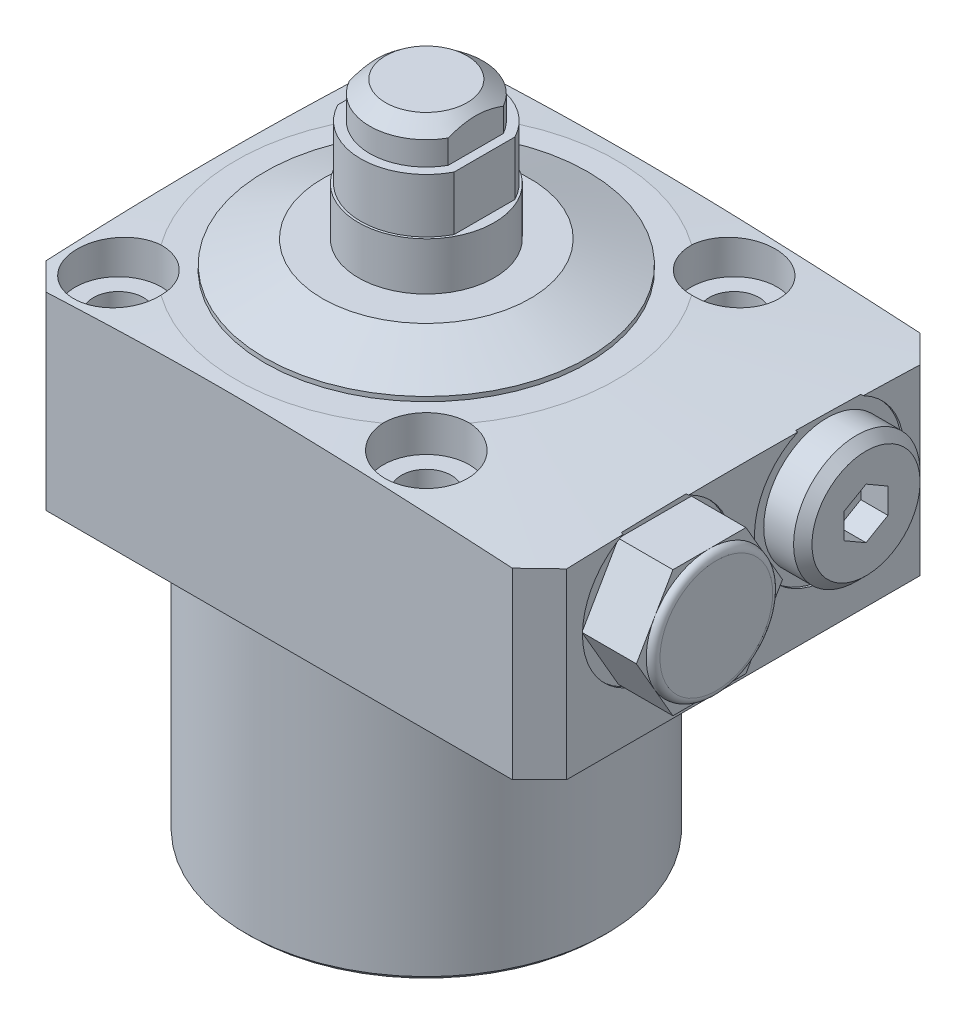
SolidWorks part; units mm, degrees
material "Alloy Steel"
ref_plane "Front Plane" through (0, 0, 0) normal (0, 0, 1) x (1, 0, 0)
ref_plane "Top Plane" through (0, 0, 0) normal (0, 1, 0) x (1, 0, 0)
ref_plane "Right Plane" through (0, 0, 0) normal (1, 0, 0) x (0, 0, -1)
sketch "Sketch1" plane through (0, 0, 0) normal (0, 0, 1) x (1, 0, 0)
  line L0 (0, 0) -> (0, -9.6761) construction
  line L1 (-19.925, 0) -> (-50, 0)
  line L2 (-50, 0) -> (-50, 19.4721)
  line L8 (-19.925, -32.5) -> (-19.925, 0)
  line L9 (-50, 19.4721) -> (-21, 21.5)
  line L10 (-21, 21.5) -> (0, 21.5)
  line L11 (0, 21.5) -> (0, -32.5)
  line L13 (-19.925, -32.5) -> (0, -32.5)
  dimension "D2" = 32.5
  dimension "D3" = 50
  dimension "D7" = 54
  dimension "D8" = 4
  dimension "D9" = 42
  dimension "D10" = 39.85
revolve "Revolve1" add sketch "Sketch1" angle 360 about L0
sketch "Sketch2" plane through (0, 21.5, 0) normal (0, 1, 0) x (1, 0, 0)
  line L0 (0, 0) -> (0, 57.0347) construction
  line L1 (-22.5, 22.5) -> (35, 22.5)
  line L2 (-22.5, 22.5) -> (-22.5, -22.5)
  line L3 (-22.5, -22.5) -> (35, -22.5)
  line L4 (35, 22.5) -> (35, -22.5)
  line L5 (0, 0) -> (-71.4399, 0) construction
  dimension "D1" = 45
  dimension "D2" = 22.5
  dimension "D3" = 57.5
extrude "Cut-Extrude1" cut sketch "Sketch2" against normal through all flip side to cut
chamfer "Chamfer2" distance 3 angle 45 4 edges at (-22.5, 10.3717, -22.5) (35, 10.0295, -22.5) (35, 10.0295, 22.5) (-22.5, 10.3717, 22.5)
sketch "Sketch4" plane through (0, 0, 0) normal (0, 0, 1) x (1, 0, 0)
  line L0 (0, 0) -> (0, 85.9979) construction
  line L1 (0, 39.75) -> (-6.25, 39.75)
  line L2 (-6.25, 39.75) -> (-6.25, 35.762)
  line L3 (-6.25, 35.762) -> (-7.25, 35.762)
  line L4 (-7.25, 35.762) -> (-7.25, 29.782)
  line L5 (-7.25, 29.782) -> (-7.5, 29.782)
  line L6 (-7.5, 29.782) -> (-7.5, 21.5)
  line L7 (21, 21.5) -> (-21, 21.5) construction
  line L8 (-7.5, 21.5) -> (0, 21.5)
  line L9 (0, 21.5) -> (0, 39.75)
  line L12 (32, 0) -> (-19.5, 0) construction
  dimension "D1" = 39.75
  dimension "D2" = 3.988
  dimension "D3" = 12.5
  dimension "D4" = 15
  dimension "D5" = 14.5
  dimension "D6" = 9.968
revolve "Revolve2" add sketch "Sketch4" angle 360 about L0
chamfer "Chamfer1" distance 1.3715 angle 51.98 1 edges at (0, 39.75, -6.25)
sketch "Sketch5" plane through (0, 0, 0) normal (0, 0, 1) x (1, 0, 0)
  line L0 (7.25, 35.762) -> (-7.25, 35.762) construction
  line L1 (-5.46, 35.762) -> (-7.25, 35.762)
  line L2 (-5.46, 35.762) -> (-5.46, 39.75)
  line L3 (-5.46, 39.75) -> (-7.25, 39.75)
  line L4 (-7.25, 35.762) -> (-7.25, 39.75)
  line L5 (4.4959, 39.75) -> (-4.4959, 39.75) construction
  line L6 (-7.25, 35.762) -> (-7.25, 29.782) construction
  line L7 (0, 0) -> (0, 109.405) construction
  line L8 (7.25, 35.762) -> (7.25, 39.75)
  line L9 (5.46, 39.75) -> (7.25, 39.75)
  line L10 (5.46, 35.762) -> (5.46, 39.75)
  line L11 (5.46, 35.762) -> (7.25, 35.762)
  dimension "D1" = 10.92
extrude "Cut-Extrude2" cut sketch "Sketch5" against normal through all and the other way through all
sketch "Sketch6" plane through (0, 0, 0) normal (0, 0, 1) x (1, 0, 0)
  line L0 (7.25, 35.762) -> (-7.25, 35.762) construction
  line L1 (-6.425, 35.762) -> (-7.5, 35.762)
  line L2 (-6.425, 35.762) -> (-6.425, 29.782)
  line L3 (-6.425, 29.782) -> (-7.5, 29.782)
  line L4 (-7.5, 35.762) -> (-7.5, 29.782)
  line L5 (0, 0) -> (0, 83.5625) construction
  line L6 (7.5, 35.762) -> (7.5, 29.782)
  line L7 (6.425, 29.782) -> (7.5, 29.782)
  line L8 (6.425, 35.762) -> (6.425, 29.782)
  line L9 (6.425, 35.762) -> (7.5, 35.762)
  dimension "D1" = 12.85
extrude "Cut-Extrude3" cut sketch "Sketch6" against normal through all and the other way through all
sketch "Sketch10" plane through (0, 21.5, 0) normal (0, 1, 0) x (1, 0, 0)
  line L0 (0, 0) -> (0, 37.6461) construction
  line L1 (0, 0) -> (33.5022, 0) construction
  circle A0 centre (-17, 17) radius 4.75
  dimension "D1" = 9.5
  dimension "D2" = 17
  dimension "D3" = 17
extrude "Cut-Extrude4" cut sketch "Sketch10" against normal offset from surface (4 mm away) 17.5 up to face at (0, 0, 19.925)
hole_wizard "Ø5.5 (5.5) Diameter Hole1" positions "3DSketch1" profile "Sketch11" hole size "Ø5.5" standard "Ansi Metric" end condition through all
sketch3d "3DSketch1"
  circle A0 centre (-17, 17.5, -17) radius 4.75 construction
  point P0 (-17, 17.5, -17)
  point P6 (-17, 22.25, -17)
sketch "Sketch11" plane through (-17, 17.5, -17) normal (1, 0, 0) x (0, 0, 1)
  line L0 (0, 0) -> (0, 50)
  line L1 (0, 50) -> (2.75, 50)
  line L2 (2.75, 50) -> (2.75, 0)
  line L5 (2.75, 0) -> (0, 0)
  line L11 (0, -6.35) -> (0, 107.95) construction
  dimension "Thru Hole Dia." = 5.5
  dimension "Thru Hole Depth" = 50
pattern_circular "CirPattern1" count 4 over 360 about axis through (0, 0, 0) along (0, 1, 0) of "Ø5.5 (5.5) Diameter Hole1", "Cut-Extrude4"
ref_plane "Plane1" through (0, 0, -9.5) normal (0, 0, 1) x (1, 0, 0)
sketch "Sketch12" plane through (0, 0, -9.5) normal (0, 0, 1) x (1, 0, 0)
  line L0 (17.9573, 13) -> (55.5469, 13) construction
  line L2 (35, 21.255) -> (34.75, 21.255)
  line L4 (34.75, 21.255) -> (34.75, 17.953)
  line L5 (34.75, 17.953) -> (34.2166, 17.4196)
  line L6 (34.2166, 17.4196) -> (24.1836, 17.4196)
  line L7 (24.1836, 17.4196) -> (21.528, 13)
  line L8 (21.528, 13) -> (35, 13)
  line L9 (35, 13) -> (35, 21.255)
  line L10 (35, 20.1668) -> (35, 0) construction
  line L11 (-19.925, -32.5) -> (19.925, -32.5) construction
  dimension "D1" = 45.5
  dimension "D2" = 16.51
  dimension "D3" = 0.25
  dimension "D4" = 8.8392
  dimension "D5" = 59
  dimension "D6" = 10.5664
  dimension "D7" = 45
  dimension "D8" = 0.5334
revolve "Cut-Revolve2" cut sketch "Sketch12" angle 360 about L0
sketch "Sketch13" plane through (0, 0, -9.5) normal (0, 0, 1) x (1, 0, 0)
  line L0 (10.4663, 13) -> (36.2703, 13) construction
  line L1 (34.2166, 13) -> (24.1836, 13) construction
  line L3 (34.75, 19.985) -> (38.045, 19.985)
  line L4 (34.75, 4.745) -> (34.75, 20.5019) construction
  line L5 (38.045, 19.985) -> (39.06, 18.97)
  line L6 (39.06, 18.97) -> (39.06, 13)
  line L7 (39.06, 13) -> (34.75, 13)
  line L8 (34.75, 13) -> (34.75, 19.985)
  dimension "D1" = 4.31
  dimension "D2" = 13.97
  dimension "D3" = 45
  dimension "D4" = 1.015
revolve "Revolve3" add sketch "Sketch13" angle 360 about L0
sketch "Sketch14" plane through (39.06, 0, 0) normal (1, 0, 0) x (0, 0, -1)
  line L1 (11.9255, 11.5996) -> (11.9255, 14.4004)
  line L2 (11.9255, 14.4004) -> (9.5, 15.8007)
  line L3 (9.5, 15.8007) -> (7.0745, 14.4004)
  line L4 (7.0745, 14.4004) -> (7.0745, 11.5996)
  line L5 (7.0745, 11.5996) -> (9.5, 10.1993)
  line L6 (9.5, 10.1993) -> (11.9255, 11.5996)
  circle A0 centre (9.5, 13) radius 2.4255 construction
  dimension "D1" = 4.851
extrude "Cut-Extrude5" cut sketch "Sketch14" against normal blind 3
sketch "Sketch16" plane through (9.5, 0, -9.5) normal (0, 0, -1) x (-1, 0, 0)
  line L0 (-17.5, -1.224) -> (-17.5, -24.6754) construction
  line L1 (-17.5, 13.5022) -> (-20, 12)
  line L2 (-20, 12) -> (-20, 2.875)
  line L3 (-20, 2.875) -> (-20.625, 2.25)
  line L4 (-20.625, 2.25) -> (-22.5, 2.25)
  line L5 (-22.5, 2.25) -> (-22.5, 0)
  line L7 (-22.5, 0) -> (-17.5, 0)
  line L8 (-17.5, 0) -> (-17.5, 13.5022)
  line L9 (9.5, -32.5) -> (9.5, 0) construction
  line L10 (29, 0) -> (-22.5, 0) construction
  dimension "D1" = 27
  dimension "D2" = 5
  dimension "D3" = 59
  dimension "D4" = 10
  dimension "D5" = 2.25
  dimension "D6" = 45
  dimension "D7" = 0.625
  dimension "D8" = 9.75
revolve "Cut-Revolve4" cut sketch "Sketch16" angle 360 about L0
pattern_linear "LPattern1" count 2 spacing 19 along (0, 0, 1) of "Cut-Extrude5", "Cut-Revolve2", "Cut-Revolve4"
sketch "Sketch18" plane through (-9.5, 0, -9.5) normal (0, 0, 1) x (1, 0, 0)
  line L0 (36.5, -2.5857) -> (36.5, -21.6782) construction
  line L3 (31.5, 2.25) -> (41.5, 2.25) construction
  line L4 (36.5, 2.875) -> (36.5, 8.5804) construction
  circle A0 centre (33.001, 0.75) radius 1.5
  dimension "D1" = 3
  dimension "D2" = 1.5
  dimension "D3" = 6.998
revolve "Revolve4" add sketch "Sketch18" angle 360 about L0
pattern_linear "LPattern2" count 2 spacing 19 along (0, 0, 1) of bodies 124
chamfer "Chamfer3" distance 0.5 angle 45 1 edges at (0, -32.5, 19.925)
fillet "Fillet1" radius 0.5 1 edges at (0, 0, 19.925)
ref_axis "Axis1" through (0, 29.782, 0) along (0, -1, 0)
sketch "Sketch19" plane through (0, 0, 0) normal (0, 0, 1) x (1, 0, 0)
  line L0 (7.5, 21.5) -> (17.82, 21.5)
  line L1 (21, 21.5) -> (17.0566, 21.5) construction
  line L2 (17.82, 21.5) -> (17.82, 22)
  line L3 (17.82, 22) -> (11.4734, 24.5)
  line L4 (11.4734, 24.5) -> (7.5, 24.5)
  line L5 (7.5, 21.5) -> (7.5, 29.782) construction
  line L6 (7.5, 24.5) -> (7.5, 21.5)
  line L7 (0, 29.782) -> (0, 21.5) construction
  dimension "D1" = 17.82
  dimension "D2" = 0.5
  dimension "D3" = 21.5
  dimension "D4" = 3
revolve "Revolve5" add sketch "Sketch19" angle 360 about axis through (0, 29.782, 0) along (0, -1, 0)
sketch "Sketch20" plane through (34.75, 0, 0) normal (1, 0, 0) x (0, 0, -1)
  line L1 (-1.4344, 13) -> (-5.4672, 19.985)
  line L2 (-5.4672, 19.985) -> (-13.5328, 19.985)
  line L3 (-13.5328, 19.985) -> (-17.5656, 13)
  line L4 (-17.5656, 13) -> (-13.5328, 6.015)
  line L5 (-13.5328, 6.015) -> (-5.4672, 6.015)
  line L6 (-5.4672, 6.015) -> (-1.4344, 13)
  circle A0 centre (-9.5, 13) radius 6.985 construction
  arc A1 (-13.2215, 20.3686) -> (-6.0552, 20.5019) centre (-9.5, 13) ccw
  arc A2 (-13.2215, 20.3686) -> (-6.0552, 20.5019) centre (-9.5, 13) ccw
  spline S1 degree 3 poles (752.2522, -2836.2075) (151.8478, 2917.5495) (-257.6915, -2865.1301) (-857.0754, 2826.9484) knots -99.190671 -99.190671 -99.190671 -99.190671 112.24011 112.24011 112.24011 112.24011 only from (-6.0552, 20.5019) to (-13.2215, 20.3686)
  spline S2 degree 3 poles (-6.0552, 20.5019) (-8.4442, 20.4732) (-10.833, 20.428) (-13.2215, 20.3686) knots 0 0 0 0 1 1 1 1
  dimension "D2" = 13.97
  dimension "D1" = 0
extrude "Boss-Extrude1" add sketch "Sketch20" along normal blind 6.78 contours L5 L6 L1 L2 L3 L4
ref_plane "Plane2" through (0, 0, 9.5) normal (0, 0, -1) x (-1, 0, 0)
sketch "Sketch21" plane through (0, 0, 9.5) normal (0, 0, -1) x (-1, 0, 0)
  line L5 (-41.53, 19.223) -> (-44.806, 19.223)
  line L6 (-40.768, 19.985) -> (-40.768, 23.1738)
  line L7 (-40.768, 23.1738) -> (-44.806, 23.1738)
  line L8 (-44.806, 19.223) -> (-44.806, 23.1738)
  arc A0 (-40.768, 19.985) -> (-41.53, 19.223) centre (-40.768, 19.223) ccw
revolve "Cut-Revolve5" cut sketch "Sketch21" angle 360 about axis through (17.9573, 13, 9.5) along (-1, 0, 0)
